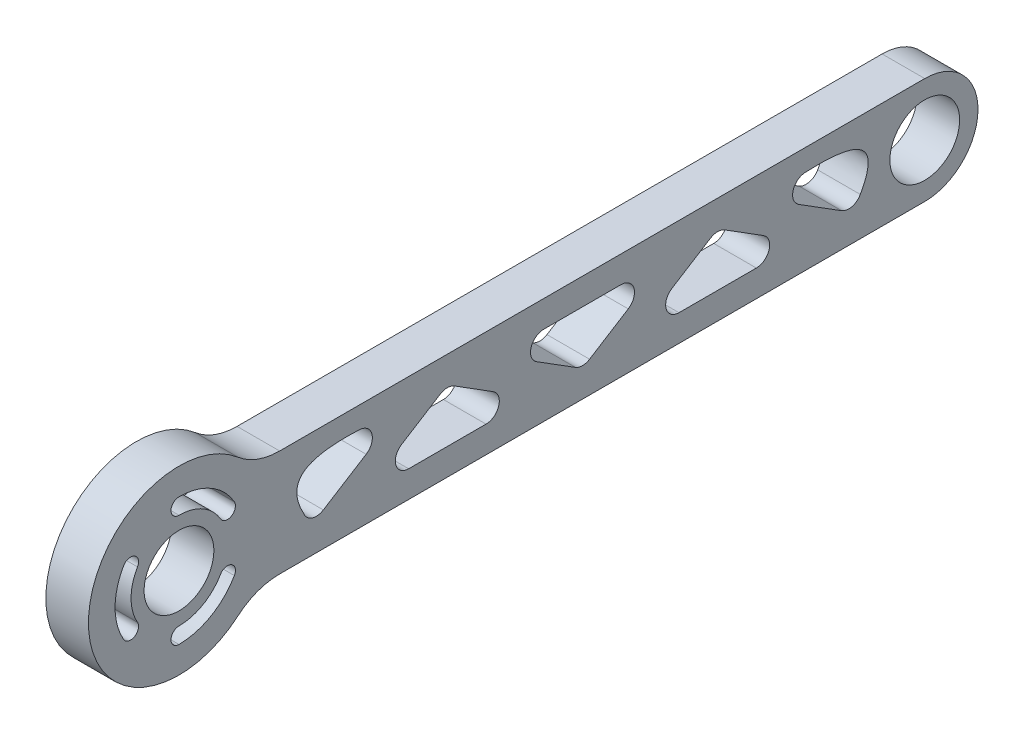
SolidWorks part; units mm, degrees
material "Thornel Mat VMA"
ref_plane "前视基准面" through (0, 0, 0) normal (0, 0, 1) x (1, 0, 0)
ref_plane "上视基准面" through (0, 0, 0) normal (0, 1, 0) x (1, 0, 0)
ref_plane "右视基准面" through (0, 0, 0) normal (1, 0, 0) x (0, 0, -1)
ref_plane "基准面4" through (-4, 0, 0) normal (-1, 0, 0) x (0, -1, 0)
sketch "草图1" plane through (-4, 0, 0) normal (-1, 0, 0) x (0, -1, 0)
  line L0 (-4.1682, -99.7975) -> (0.3816, -92.5368)
  line L1 (5, -93.8643) -> (5, -108.3857)
  line L2 (0.3816, -109.7132) -> (-4.1682, -102.4525)
  line L3 (-1.3479, -116.3696) -> (3.6833, -124.3987)
  line L4 (0.3816, -58.9632) -> (-4.1682, -51.7025)
  line L5 (-4.1682, -49.0475) -> (0.3816, -41.7868)
  line L6 (5, -43.1143) -> (5, -57.6357)
  line L7 (3.6833, -27.1013) -> (-1.3479, -35.1304)
  line L8 (4.1682, -77.0775) -> (-0.3816, -84.3382)
  line L9 (-5, -83.0107) -> (-5, -68.4893)
  line L10 (-0.3816, -67.1618) -> (4.1682, -74.4225)
  line L11 (-10, -18.8944) -> (-10, -140)
  line L12 (10, -140) -> (10, -18.8944)
  arc A0 (-4.1682, -102.4525) -> (-4.1682, -99.7975) centre (-2.0497, -101.125) cw
  arc A1 (0.3816, -92.5368) -> (5, -93.8643) centre (2.5, -93.8643) cw
  arc A2 (5, -108.3857) -> (0.3816, -109.7132) centre (2.5, -108.3857) cw
  arc A3 (-5.9631, -117.5695) -> (-1.3479, -116.3696) centre (-3.4664, -117.6971) cw
  arc A4 (3.6833, -124.3987) -> (2.7929, -127.9037) centre (1.5648, -125.7262) cw
  arc A5 (5, -57.6357) -> (0.3816, -58.9632) centre (2.5, -57.6357) cw
  arc A6 (-4.1682, -51.7025) -> (-4.1682, -49.0475) centre (-2.0497, -50.375) cw
  arc A7 (0.3816, -41.7868) -> (5, -43.1143) centre (2.5, -43.1143) cw
  arc A8 (-1.3479, -35.1304) -> (-5.9631, -33.9305) centre (-3.4664, -33.8029) cw
  arc A9 (2.7929, -23.5963) -> (3.6833, -27.1013) centre (1.5648, -25.7738) cw
  arc A10 (4.1682, -74.4225) -> (4.1682, -77.0775) centre (2.0497, -75.75) cw
  arc A11 (-0.3816, -84.3382) -> (-5, -83.0107) centre (-2.5, -83.0107) cw
  arc A12 (-5, -68.4893) -> (-0.3816, -67.1618) centre (-2.5, -68.4893) cw
  circle A13 centre (0, -140) radius 6.55
  arc A14 (10, -18.8944) -> (12.8966, -11.0761) centre (22, -18.8944) cw
  arc A15 (12.8966, -11.0761) -> (-12.8966, -11.0761) centre (0, 0) ccw
  arc A16 (-12.8966, -11.0761) -> (-10, -18.8944) centre (-22, -18.8944) cw
  arc A17 (-10, -140) -> (10, -140) centre (0, -140) ccw
  arc A18 (-4.5, 7.7942) -> (-6, 10.3923) centre (-5.25, 9.0933) cw
  arc A19 (-6, 10.3923) -> (6, 10.3923) centre (0, 0) cw
  arc A20 (6, 10.3923) -> (4.5, 7.7942) centre (5.25, 9.0933) cw
  arc A21 (4.5, 7.7942) -> (-4.5, 7.7942) centre (0, 0) ccw
  arc A22 (9, 0) -> (12, 0) centre (10.5, 0) cw
  arc A23 (12, 0) -> (6, -10.3923) centre (0, 0) cw
  arc A24 (6, -10.3923) -> (4.5, -7.7942) centre (5.25, -9.0933) cw
  arc A25 (4.5, -7.7942) -> (9, 0) centre (0, 0) ccw
  arc A26 (-4.5, -7.7942) -> (-6, -10.3923) centre (-5.25, -9.0933) cw
  arc A27 (-6, -10.3923) -> (-12, 0) centre (0, 0) cw
  arc A28 (-12, 0) -> (-9, 0) centre (-10.5, 0) cw
  arc A29 (-9, 0) -> (-4.5, -7.7942) centre (0, 0) ccw
  circle A30 centre (0, 0) radius 6.55
  spline S0 degree 3 poles (2.7929, -127.9037) (-2.8776, -131.1016) (-5.9854, -127.8082) (-6.0768, -119.7933) (-5.9631, -117.5695) knots 0.005409 0.005409 0.005409 0.005409 0.69354 0.980498 0.980498 0.980498 0.980498
  spline S1 degree 3 poles (-5.9631, -33.9305) (-6.0768, -31.7067) (-5.9854, -23.6918) (-2.8776, -20.3984) (2.7929, -23.5963) knots 0.005409 0.005409 0.005409 0.005409 0.292367 0.980498 0.980498 0.980498 0.980498
extrude "凸台-拉伸1" add sketch "草图1" against normal blind 8
